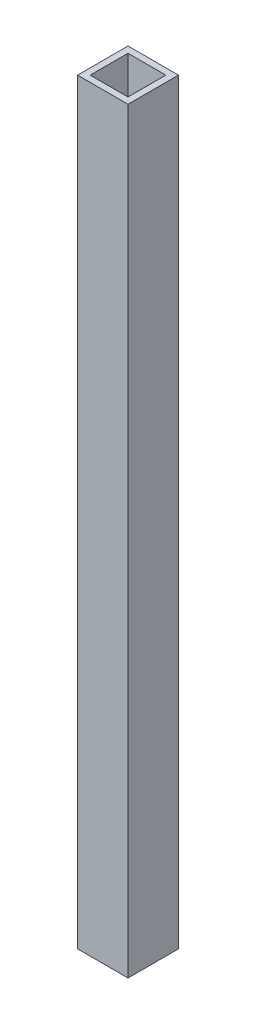
SolidWorks part; units mm, degrees
ref_plane "Front" through (0, 0, 0) normal (0, 0, 1) x (1, 0, 0)
ref_plane "Top" through (0, 0, 0) normal (0, 1, 0) x (1, 0, 0)
ref_plane "Right" through (0, 0, 0) normal (1, 0, 0) x (0, 0, -1)
sketch "Sketch1" plane through (0, 0, 0) normal (0, 1, 0) x (1, 0, 0)
  line L0 (1.5875, 1.5875) -> (11.1125, 1.5875)
  line L1 (0, 0) -> (12.7, 0)
  line L2 (0, 0) -> (0, 12.7)
  line L3 (0, 12.7) -> (12.7, 12.7)
  line L4 (12.7, 0) -> (12.7, 12.7)
  line L5 (11.1125, 1.5875) -> (11.1125, 11.1125)
  line L6 (1.5875, 11.1125) -> (11.1125, 11.1125)
  line L7 (1.5875, 1.5875) -> (1.5875, 11.1125)
  dimension "D1" = 1.5875
extrude "Boss-Extrude1" add sketch "Sketch1" along normal blind 190.5
